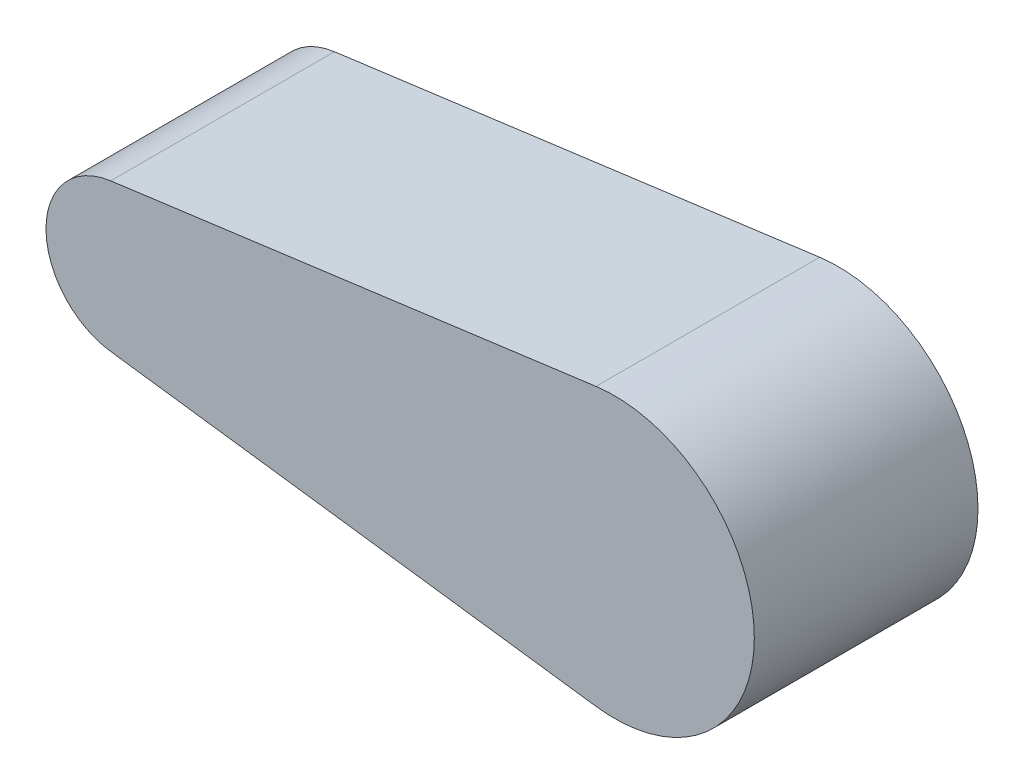
SolidWorks part; units mm, degrees
ref_plane "Front Plane" through (0, 0, 0) normal (0, 0, 1) x (1, 0, 0)
ref_plane "Top Plane" through (0, 0, 0) normal (0, 1, 0) x (1, 0, 0)
ref_plane "Right Plane" through (0, 0, 0) normal (1, 0, 0) x (0, 0, -1)
sketch "Sketch1" plane through (0, 0, 0) normal (0, 0, 1) x (1, 0, 0)
  line L0 (-155.283, 39.6496) -> (105.0943, 74.343)
  line L1 (-190, 75) -> (190, 75) construction
  line L2 (-190, 75) -> (-190, -75) construction
  line L3 (-190, -75) -> (190, -75) construction
  line L4 (190, 75) -> (190, -75) construction
  line L5 (-154.3077, -39.7674) -> (105.0909, -74.3425)
  arc A0 (105.0909, -74.3425) -> (105.0943, 74.343) centre (115, 0) ccw
  arc A1 (-155.283, 39.6496) -> (-154.3077, -39.7674) centre (-150, 0) ccw
  point P4 (0, 75)
  point P6 (-190, 0)
  dimension "D3" = 80
  dimension "D1" = 380
  dimension "D2" = 150
extrude "Extrude1" add sketch "Sketch1" along normal blind 120
